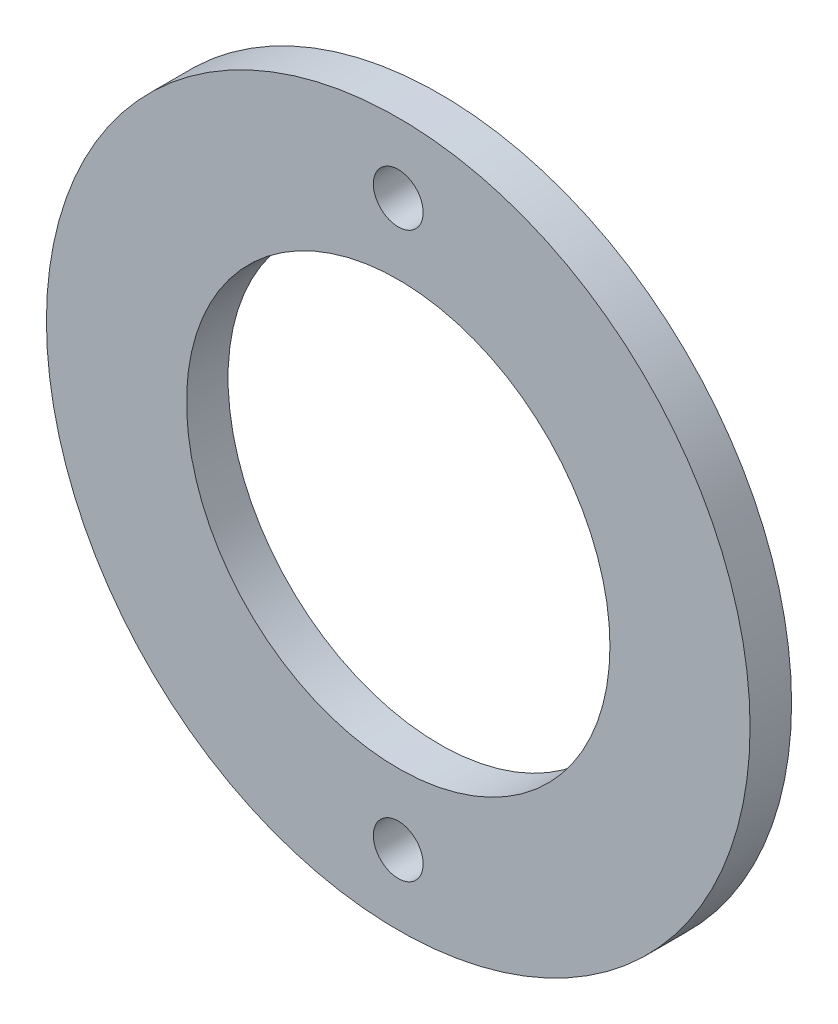
SolidWorks part; units mm, degrees
ref_plane "Front Plane" through (0, 0, 0) normal (0, 0, 1) x (1, 0, 0)
ref_plane "Top Plane" through (0, 0, 0) normal (0, 1, 0) x (1, 0, 0)
ref_plane "Right Plane" through (0, 0, 0) normal (1, 0, 0) x (0, 0, -1)
sketch "Sketch1" plane through (0, 0, 0) normal (0, 0, 1) x (1, 0, 0)
  circle A0 centre (0, 0) radius 16.2
  circle A1 centre (0, 0) radius 26.924
  circle A2 centre (0, 21.59) radius 1.905
  circle A3 centre (0, -21.59) radius 1.905
  dimension "D1" = 32.4
  dimension "D2" = 53.848
  dimension "D3" = 3.81
  dimension "D6" = 3.81
  dimension "D4" = 21.59
  dimension "D5" = 21.59
extrude "Boss-Extrude1" add sketch "Sketch1" along normal blind 3.175
